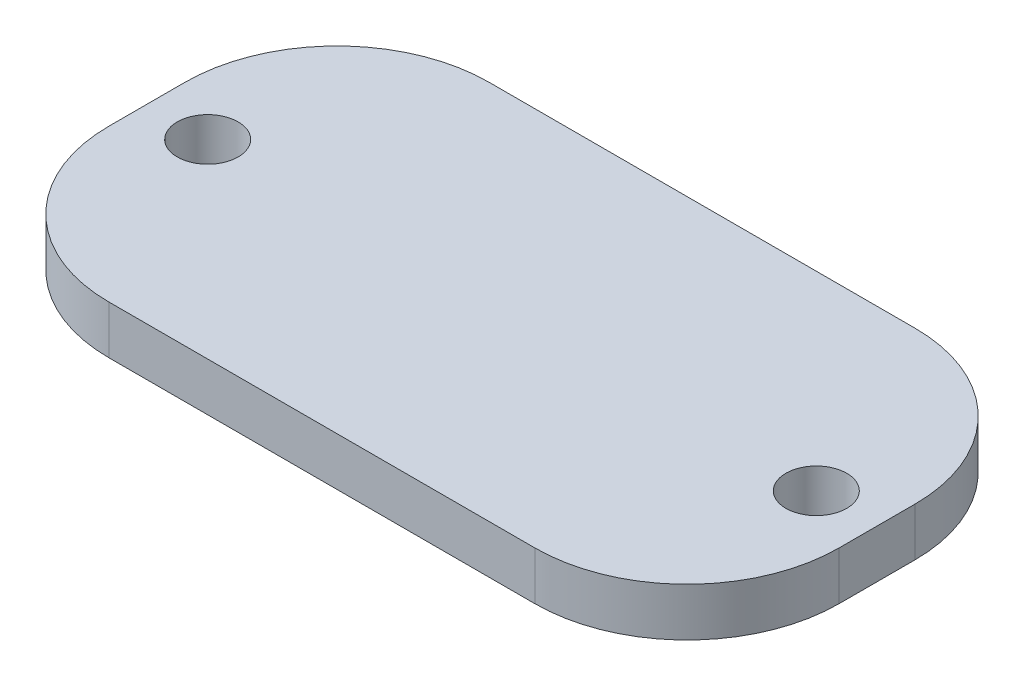
SolidWorks part; units mm, degrees
ref_plane "Front Plane" through (0, 0, 0) normal (0, 0, 1) x (1, 0, 0)
ref_plane "Top Plane" through (0, 0, 0) normal (0, 1, 0) x (1, 0, 0)
ref_plane "Right Plane" through (0, 0, 0) normal (1, 0, 0) x (0, 0, -1)
sketch "Sketch1" plane through (0, 0, 0) normal (0, 1, 0) x (1, 0, 0)
  line L1 (-24, 12.5) -> (24, 12.5)
  line L2 (-24, 12.5) -> (-24, -12.5)
  line L3 (-24, -12.5) -> (24, -12.5)
  line L4 (24, 12.5) -> (24, -12.5)
  line L5 (-24, 12.5) -> (24, -12.5) construction
  line L6 (-24, -12.5) -> (24, 12.5) construction
  circle A0 centre (-20, 0) radius 2
  circle A1 centre (20, 0) radius 2
  point P0 (0, 0)
  dimension "D1" = 4
  dimension "D2" = 25
  dimension "D3" = 20
  dimension "D4" = 20
  dimension "D5" = 48
extrude "Boss-Extrude1" add sketch "Sketch1" along normal blind 3.175
fillet "Fillet1" radius 10 4 edges at (-24, 1.5875, 12.5) (24, 1.5875, 12.5) (24, 1.5875, -12.5) (-24, 1.5875, -12.5)
